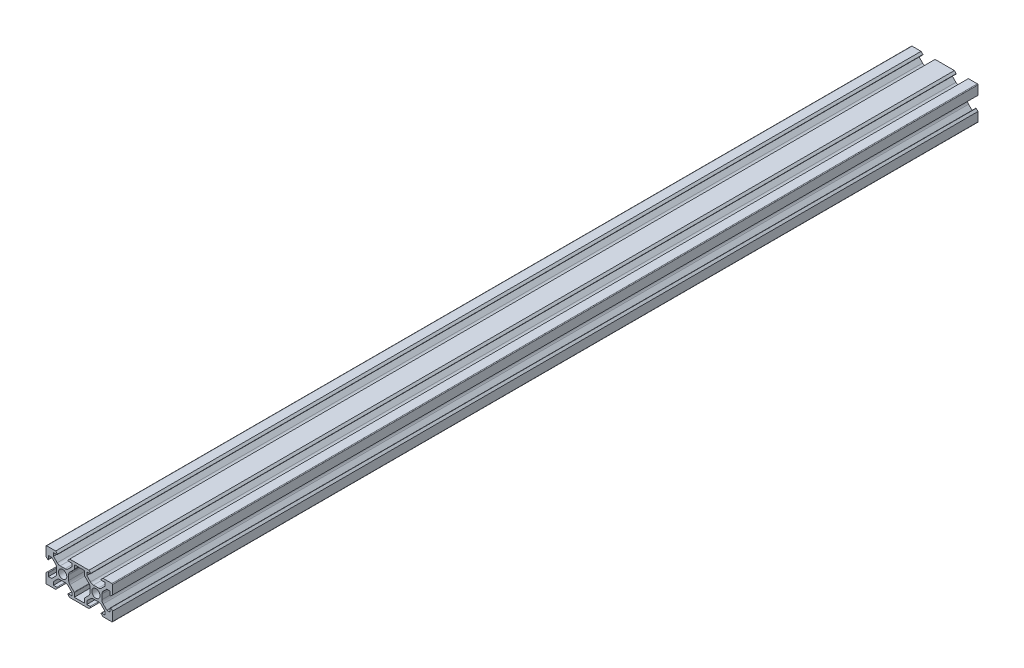
SolidWorks part; units mm, degrees
material "6063-T5"
ref_plane "Plano frontal" through (0, 0, 0) normal (0, 0, 1) x (1, 0, 0)
ref_plane "Plano superior" through (0, 0, 0) normal (0, 1, 0) x (1, 0, 0)
ref_plane "Plano direito" through (0, 0, 0) normal (1, 0, 0) x (0, 0, -1)
sketch "Esboço1" plane through (0, 0, 0) normal (0, 0, 1) x (1, 0, 0)
  line L0 (-13.1, 8.9) -> (-14.2, 10)
  line L1 (-19.6, 10) -> (-14.2, 10)
  line L2 (-13.6, 1.5038) -> (-13.6, 0)
  line L3 (-18.5, 5.5) -> (-18.5, 3.5)
  line L4 (-16.5607, 5.5) -> (-14.3322, 3.2716)
  line L5 (-18.5, 5.5) -> (-16.5607, 5.5)
  line L6 (-20, 9.6) -> (-20, 4.2)
  line L7 (-18.9, 3.1) -> (-20, 4.2)
  line L8 (-3, 8.5) -> (3, 8.5)
  line L9 (-3.1172, 5.8222) -> (-5.6678, 3.2716)
  line L10 (-8.4962, 3.6) -> (-10, 3.6)
  line L11 (-8.2322, 1.7678) -> (-10, 0) construction
  line L12 (-4.5, 6.5607) -> (-6.7284, 4.3322)
  line L13 (-15.5, 8.5) -> (-15.5, 6.5607)
  line L14 (-4.5, 8.5) -> (-4.5, 6.5607)
  line L15 (0, 0) -> (0, 8.5) construction
  line L16 (-6.9, 8.9) -> (-5.8, 10)
  line L17 (-6.4, 0) -> (6.4, 0) construction
  line L18 (-3, -8.5) -> (-3, -6.105)
  line L19 (-18.5, 8.5) -> (-18.5, -8.5) construction
  line L20 (-3.1172, -5.8222) -> (-5.6678, -3.2716)
  line L21 (-6.4, 1.5038) -> (-6.4, 0)
  line L22 (-5.8, -10) -> (5.8, -10)
  line L23 (-19.8828, 9.8828) -> (-10, 0) construction
  line L24 (-6.9, -8.9) -> (-5.8, -10)
  line L25 (-15.5, 6.5607) -> (-13.2716, 4.3322)
  line L26 (-3, -8.5) -> (3, -8.5)
  line L27 (-20, 10) -> (-20, -10) construction
  line L28 (-6.4, -1.5038) -> (-6.4, 0)
  line L29 (19.8828, -9.8828) -> (10, 0) construction
  line L30 (8.2322, -1.7678) -> (10, 0) construction
  line L31 (19.8828, 9.8828) -> (10, 0) construction
  line L32 (8.2322, 1.7678) -> (10, 0) construction
  line L33 (-15.5, 8.5) -> (-13.5, 8.5)
  line L34 (6.5, 8.5) -> (4.5, 8.5)
  line L35 (-4.5, -8.5) -> (-4.5, -6.5607)
  line L36 (-20, 10) -> (0, 10) construction
  line L37 (-4.5, -6.5607) -> (-6.7284, -4.3322)
  line L38 (-4.5, -8.5) -> (-6.5, -8.5)
  line L39 (-18.5, 8.5) -> (-1.5, 8.5) construction
  line L40 (-11.5038, 3.6) -> (-10, 3.6)
  line L41 (-8.4962, -3.6) -> (-10, -3.6)
  line L42 (-8.2322, -1.7678) -> (-10, 0) construction
  line L43 (-18.9, -3.1) -> (-20, -4.2)
  line L44 (-20, -9.6) -> (-20, -4.2)
  line L45 (-11.5038, -3.6) -> (-10, -3.6)
  line L46 (-15.5, -8.5) -> (-13.5, -8.5)
  line L47 (-15.5, -6.5607) -> (-13.2716, -4.3322)
  line L48 (-15.5, -8.5) -> (-15.5, -6.5607)
  line L49 (-19.6, -10) -> (-14.2, -10)
  line L50 (-13.1, -8.9) -> (-14.2, -10)
  line L51 (-18.5, -5.5) -> (-16.5607, -5.5)
  line L52 (-16.5607, -5.5) -> (-14.3322, -3.2716)
  line L53 (-18.5, -5.5) -> (-18.5, -3.5)
  line L54 (0, 10) -> (0, -10) construction
  line L55 (-20, -10) -> (0, -10) construction
  line L56 (-13.6, -1.5038) -> (-13.6, 0)
  line L57 (-18.5, -8.5) -> (-1.5, -8.5) construction
  line L58 (-1.5, 8.5) -> (-1.5, -8.5) construction
  line L59 (-19.8828, -9.8828) -> (-10, 0) construction
  line L60 (3, 8.5) -> (3, 6.105)
  line L61 (-3, 8.5) -> (-3, 6.105)
  line L62 (-6.5, 8.5) -> (-4.5, 8.5)
  line L63 (-5.8, 10) -> (5.8, 10)
  line L64 (13.6, -1.5038) -> (13.6, 0)
  line L65 (18.5, -5.5) -> (18.5, -3.5)
  line L66 (16.5607, -5.5) -> (14.3322, -3.2716)
  line L67 (18.5, -5.5) -> (16.5607, -5.5)
  line L68 (13.1, -8.9) -> (14.2, -10)
  line L69 (19.6, -10) -> (14.2, -10)
  line L70 (15.5, -8.5) -> (15.5, -6.5607)
  line L71 (15.5, -6.5607) -> (13.2716, -4.3322)
  line L72 (15.5, -8.5) -> (13.5, -8.5)
  line L73 (11.5038, -3.6) -> (10, -3.6)
  line L74 (20, -9.6) -> (20, -4.2)
  line L75 (18.9, -3.1) -> (20, -4.2)
  line L76 (8.4962, -3.6) -> (10, -3.6)
  line L77 (11.5038, 3.6) -> (10, 3.6)
  line L78 (4.5, -8.5) -> (6.5, -8.5)
  line L79 (4.5, -6.5607) -> (6.7284, -4.3322)
  line L80 (4.5, -8.5) -> (4.5, -6.5607)
  line L81 (15.5, 8.5) -> (13.5, 8.5)
  line L82 (6.4, -1.5038) -> (6.4, 0)
  line L83 (15.5, 6.5607) -> (13.2716, 4.3322)
  line L84 (6.9, -8.9) -> (5.8, -10)
  line L85 (6.4, 1.5038) -> (6.4, 0)
  line L86 (3.1172, -5.8222) -> (5.6678, -3.2716)
  line L87 (3, -8.5) -> (3, -6.105)
  line L88 (6.9, 8.9) -> (5.8, 10)
  line L89 (4.5, 8.5) -> (4.5, 6.5607)
  line L90 (15.5, 8.5) -> (15.5, 6.5607)
  line L91 (4.5, 6.5607) -> (6.7284, 4.3322)
  line L92 (8.4962, 3.6) -> (10, 3.6)
  line L93 (3.1172, 5.8222) -> (5.6678, 3.2716)
  line L94 (18.9, 3.1) -> (20, 4.2)
  line L95 (20, 9.6) -> (20, 4.2)
  line L96 (18.5, 5.5) -> (16.5607, 5.5)
  line L97 (16.5607, 5.5) -> (14.3322, 3.2716)
  line L98 (18.5, 5.5) -> (18.5, 3.5)
  line L99 (13.6, 1.5038) -> (13.6, 0)
  line L100 (19.6, 10) -> (14.2, 10)
  line L101 (13.1, 8.9) -> (14.2, 10)
  arc A0 (-10, 2.5) -> (-12.5, 0) centre (-10, 0) ccw
  arc A1 (-13.5, 8.5) -> (-13.1, 8.9) centre (-13.5, 8.9) ccw
  arc A2 (-19.6, 10) -> (-20, 9.6) centre (-19.6, 9.6) ccw
  arc A3 (-13.2716, 4.3322) -> (-11.5038, 3.6) centre (-11.5038, 6.1) ccw
  arc A4 (-14.3322, 3.2716) -> (-13.6, 1.5038) centre (-16.1, 1.5038) cw
  arc A5 (-18.5, 3.5) -> (-18.9, 3.1) centre (-18.9, 3.5) cw
  arc A6 (-7.5, 0) -> (-10, 2.5) centre (-10, 0) ccw
  arc A7 (-3, -6.105) -> (-3.1172, -5.8222) centre (-3.4, -6.105) ccw
  arc A8 (-3.1172, 5.8222) -> (-3, 6.105) centre (-3.4, 6.105) ccw
  arc A9 (-5.6678, 3.2716) -> (-6.4, 1.5038) centre (-3.9, 1.5038) ccw
  arc A10 (-6.7284, 4.3322) -> (-8.4962, 3.6) centre (-8.4962, 6.1) cw
  arc A11 (-6.5, 8.5) -> (-6.9, 8.9) centre (-6.5, 8.9) cw
  arc A12 (-10, -2.5) -> (-7.5, 0) centre (-10, 0) ccw
  arc A13 (-6.5, -8.5) -> (-6.9, -8.9) centre (-6.5, -8.9) ccw
  arc A14 (13.5, -8.5) -> (13.1, -8.9) centre (13.5, -8.9) ccw
  arc A15 (-6.7284, -4.3322) -> (-8.4962, -3.6) centre (-8.4962, -6.1) ccw
  arc A16 (-5.6678, -3.2716) -> (-6.4, -1.5038) centre (-3.9, -1.5038) cw
  arc A17 (13.2716, -4.3322) -> (11.5038, -3.6) centre (11.5038, -6.1) ccw
  arc A18 (-12.5, 0) -> (-10, -2.5) centre (-10, 0) ccw
  arc A19 (-18.5, -3.5) -> (-18.9, -3.1) centre (-18.9, -3.5) ccw
  arc A20 (-20, -9.6) -> (-19.6, -10) centre (-19.6, -9.6) ccw
  arc A21 (-14.3322, -3.2716) -> (-13.6, -1.5038) centre (-16.1, -1.5038) ccw
  arc A22 (-13.2716, -4.3322) -> (-11.5038, -3.6) centre (-11.5038, -6.1) cw
  arc A23 (-13.5, -8.5) -> (-13.1, -8.9) centre (-13.5, -8.9) cw
  arc A24 (14.3322, -3.2716) -> (13.6, -1.5038) centre (16.1, -1.5038) cw
  arc A25 (20, -9.6) -> (19.6, -10) centre (19.6, -9.6) cw
  arc A26 (18.5, -3.5) -> (18.9, -3.1) centre (18.9, -3.5) cw
  arc A27 (12.5, 0) -> (10, -2.5) centre (10, 0) cw
  arc A28 (5.6678, -3.2716) -> (6.4, -1.5038) centre (3.9, -1.5038) ccw
  arc A29 (6.7284, -4.3322) -> (8.4962, -3.6) centre (8.4962, -6.1) cw
  arc A30 (6.5, -8.5) -> (6.9, -8.9) centre (6.5, -8.9) cw
  arc A31 (10, -2.5) -> (7.5, 0) centre (10, 0) cw
  arc A32 (6.5, 8.5) -> (6.9, 8.9) centre (6.5, 8.9) ccw
  arc A33 (6.7284, 4.3322) -> (8.4962, 3.6) centre (8.4962, 6.1) ccw
  arc A34 (5.6678, 3.2716) -> (6.4, 1.5038) centre (3.9, 1.5038) cw
  arc A35 (3.1172, 5.8222) -> (3, 6.105) centre (3.4, 6.105) cw
  arc A36 (3, -6.105) -> (3.1172, -5.8222) centre (3.4, -6.105) cw
  arc A37 (7.5, 0) -> (10, 2.5) centre (10, 0) cw
  arc A38 (18.5, 3.5) -> (18.9, 3.1) centre (18.9, 3.5) ccw
  arc A39 (14.3322, 3.2716) -> (13.6, 1.5038) centre (16.1, 1.5038) ccw
  arc A40 (13.2716, 4.3322) -> (11.5038, 3.6) centre (11.5038, 6.1) cw
  arc A41 (19.6, 10) -> (20, 9.6) centre (19.6, 9.6) cw
  arc A42 (13.5, 8.5) -> (13.1, 8.9) centre (13.5, 8.9) cw
  arc A43 (10, 2.5) -> (12.5, 0) centre (10, 0) cw
  point P116 (-10, 0)
  point P168 (0, 10)
  point P183 (0, -8.5)
  point P185 (0, -10)
  dimension "D4" = 2.5
  dimension "D1" = 0.4
  dimension "D3" = 0.4
  dimension "D5" = 0.4
  dimension "D2" = 45
extrude "Ressalto-extrusão1" add sketch "Esboço1" along normal mid plane 520
